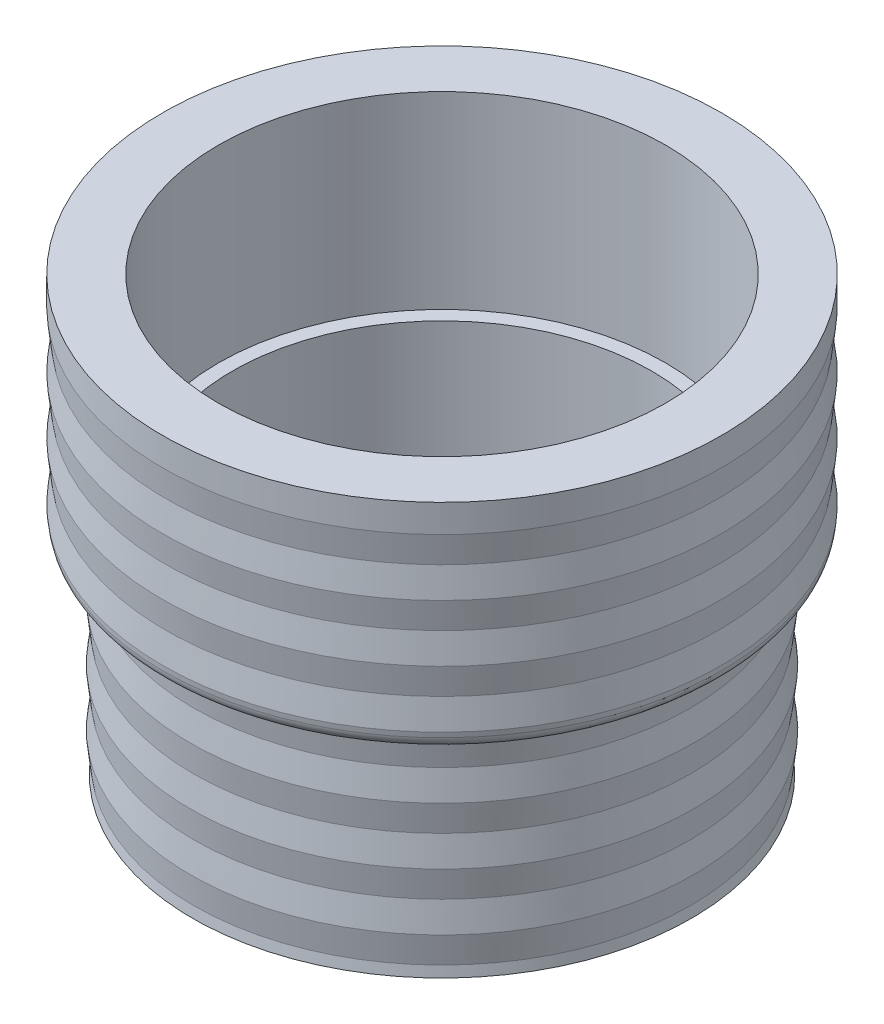
SolidWorks part; units mm, degrees
ref_plane "Front Plane" through (0, 0, 0) normal (0, 0, 1) x (1, 0, 0)
ref_plane "Top Plane" through (0, 0, 0) normal (0, 1, 0) x (1, 0, 0)
ref_plane "Right Plane" through (0, 0, 0) normal (1, 0, 0) x (0, 0, -1)
sketch "Sketch2" plane through (0, 0, 0) normal (0, 0, 1) x (1, 0, 0)
  line L1 (25.4, 49.2125) -> (31.75, 49.2125)
  line L2 (31.75, 49.2125) -> (31.75, 24.6062)
  line L4 (0, -40.6566) -> (0, 40.6566)
  line L5 (22.225, 0) -> (28.575, 0)
  line L6 (28.575, 0) -> (28.575, 24.6062)
  line L7 (28.575, 24.6062) -> (31.75, 24.6062)
  line L8 (22.225, 0) -> (22.225, 6.35)
  line L9 (23.8125, 27.7812) -> (25.4, 27.7812)
  line L10 (25.4, 27.7812) -> (25.4, 49.2125)
  line L11 (22.225, 6.35) -> (23.8125, 6.35)
  line L12 (23.8125, 6.35) -> (23.8125, 27.7812)
  point P0 (30.1625, 24.6062)
  point P8 (0, 0)
  dimension "D1" = 49.2125
  dimension "D2" = 31.75
  dimension "D3" = 28.575
  dimension "D4" = 25.4
  dimension "D5" = 3.175
  dimension "D6" = 24.6062
  dimension "D7" = 6.35
  dimension "D8" = 1.5875
  dimension "D9" = 22.225
revolve "Revolve1" add sketch "Sketch2" angle 360 about L4
sketch "Sketch3" plane through (0, 0, 0) normal (0, 0, 1) x (1, 0, 0)
  line L0 (31.75, 46.0375) -> (31.369, 42.799)
  line L1 (31.75, 24.6063) -> (31.75, 49.2125) construction
  line L2 (31.369, 42.799) -> (31.75, 39.5605)
  line L3 (31.75, 46.0375) -> (31.75, 39.5605)
  line L4 (31.75, 49.2125) -> (-31.75, 49.2125) construction
  line L5 (28.575, 23.8443) -> (28.575, 17.3673)
  line L6 (28.575, 0) -> (28.575, 24.6063) construction
  line L7 (28.575, 17.3673) -> (28.194, 20.6058)
  line L8 (28.194, 20.6058) -> (28.575, 23.8443)
  line L9 (-31.75, 24.6063) -> (31.75, 24.6063) construction
  dimension "D1" = 0.381
  dimension "D2" = 6.477
  dimension "D3" = 3.175
  dimension "D4" = 0.762
revolve "Cut-Revolve1" cut sketch "Sketch3" angle 360 about L4
pattern_linear "LPattern1" count 6 spacing 6.477 along (0, -1, 0) of "Cut-Revolve1"
fillet "Fillet1" radius 1.5875 1 edges at (0, 24.6062, -31.5147)
